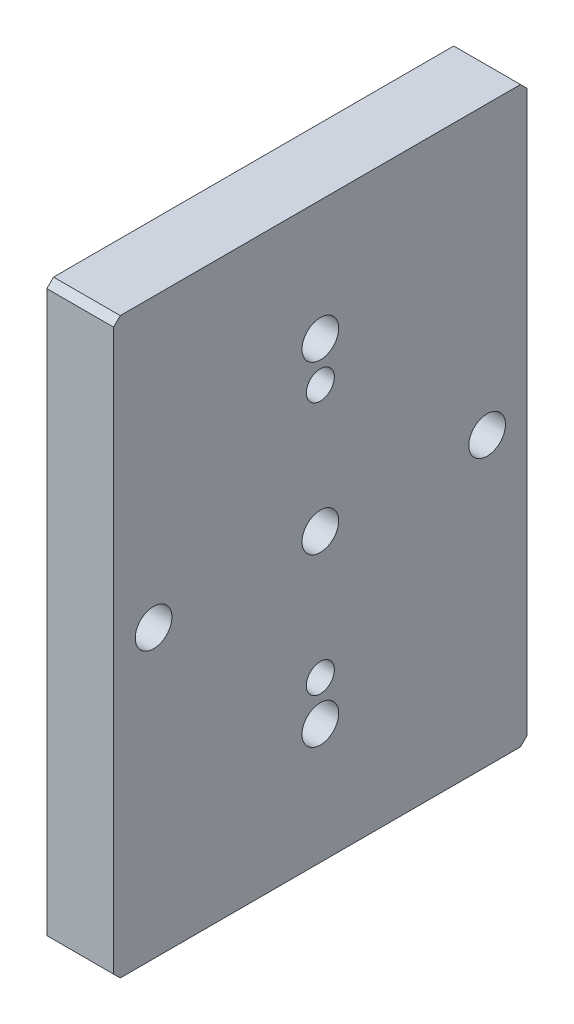
SolidWorks part; units mm, degrees
ref_plane "前视基准面" through (0, 0, 0) normal (0, 0, 1) x (1, 0, 0)
ref_plane "上视基准面" through (0, 0, 0) normal (0, 1, 0) x (1, 0, 0)
ref_plane "右视基准面" through (0, 0, 0) normal (1, 0, 0) x (0, 0, -1)
sketch "草图1" plane through (0, 0, 0) normal (1, 0, 0) x (0, 0, -1)
  line L1 (31, -43) -> (-31, -43)
  line L2 (31, -43) -> (31, 43)
  line L3 (31, 43) -> (-31, 43)
  line L4 (-31, -43) -> (-31, 43)
  line L5 (31, -43) -> (-31, 43) construction
  line L6 (31, 43) -> (-31, -43) construction
  point P0 (0, 0)
  dimension "D1" = 62
  dimension "D2" = 86
extrude "凸台-拉伸1" add sketch "草图1" along normal blind 10
chamfer "倒角1" distance 1 angle 45 4 edges at (5, 43, 31) (5, 43, -31) (5, -43, -31) (5, -43, 31)
hole_wizard "打孔尺寸(%根据)内六角圆柱头螺钉的类型1" positions "草图5" profile "草图4" counterbore size "M5" standard "GB" end condition through all
sketch "草图5" plane through (0, 0, 0) normal (-1, 0, 0) x (0, 0, 1)
  line L0 (0, 0) -> (25, 0) construction
  circle A0 centre (0, 0) radius 25 construction
  point P0 (25, 0)
  point P22 (0, -25)
  point P23 (-25, 0)
  point P24 (0, 25)
  point P25 (0, 0)
  dimension "D1" = 50
  dimension "D2" = 4
sketch "草图4" plane through (0, 0, 25) normal (0, 1, 0) x (0, 0, 1)
  line L0 (0, 0) -> (0, 10)
  line L1 (0, 10) -> (2.75, 10)
  line L3 (2.75, 10) -> (2.75, 5.5)
  line L4 (2.75, 5.5) -> (5, 5.5)
  line L5 (5, 5.5) -> (5, 0)
  line L7 (5, 0) -> (0, 0)
  line L11 (0, -6.35) -> (0, 107.95) construction
  dimension "通孔孔直径" = 5.5
  dimension "通孔孔深度" = 10
  dimension "柱形沉头孔直径" = 10
  dimension "柱形沉头孔深度" = 5.5
hole_wizard "M5 螺纹孔1" positions "草图7" profile "草图6" tap size "M5" standard "ISO" end condition through all
sketch "草图7" plane through (0, 0, 0) normal (-1, 0, 0) x (0, 0, 1)
  point P0 (0, 19)
  point P3 (0, -19)
sketch "草图6" plane through (0, 19, 0) normal (0, 1, 0) x (0, 0, 1)
  line L0 (0, 0) -> (0, 10)
  line L1 (0, 10) -> (2.1, 10)
  line L2 (2.1, 10) -> (2.1, 0)
  line L5 (2.1, 0) -> (0, 0)
  line L11 (0, -6.35) -> (0, 107.95) construction
  dimension "通孔螺纹孔钻头直径" = 4.2
  dimension "通孔螺纹孔钻头深度" = 10
cosmetic thread "孔螺蚊线1" parameters "D2"=5
cosmetic thread "孔螺蚊线2" parameters "D2"=5
